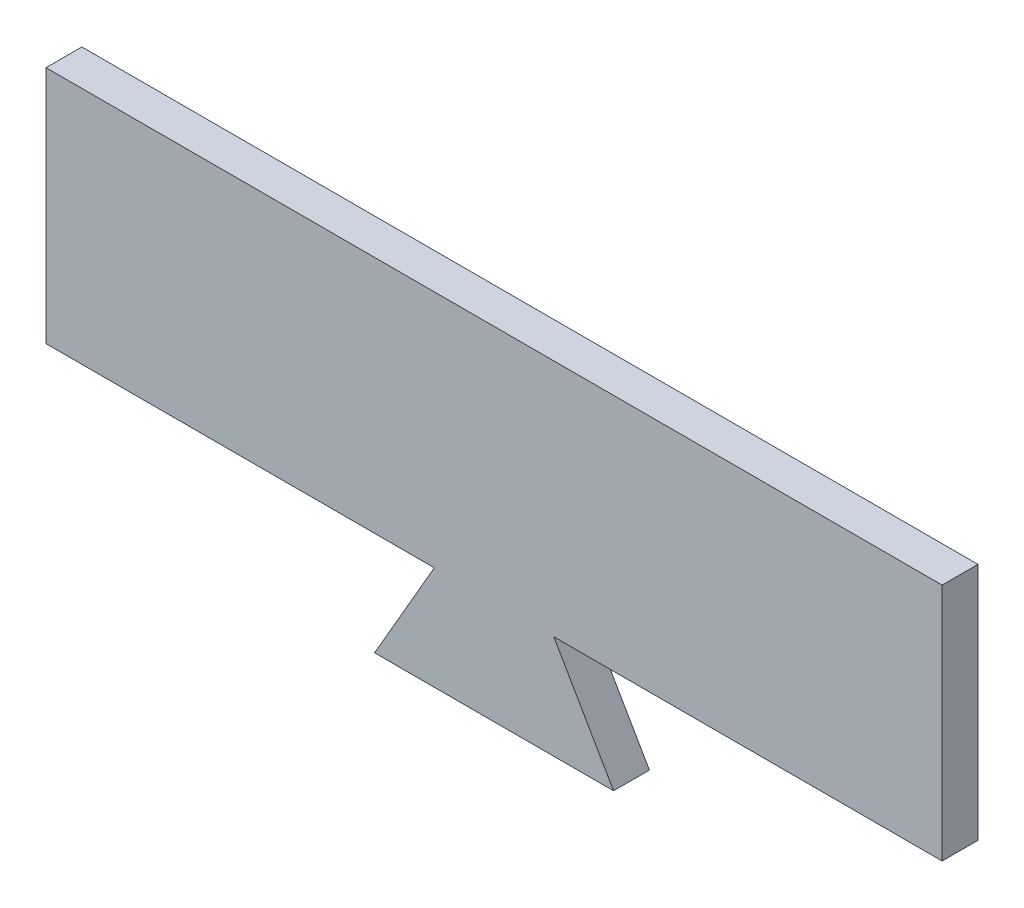
SolidWorks part; units mm, degrees
ref_plane "Plan de face" through (0, 0, 0) normal (0, 0, 1) x (1, 0, 0)
ref_plane "Plan de dessus" through (0, 0, 0) normal (0, 1, 0) x (1, 0, 0)
ref_plane "Plan de droite" through (0, 0, 0) normal (1, 0, 0) x (0, 0, -1)
sketch "Esquisse1" plane through (0, 0, 0) normal (0, 0, 1) x (1, 0, 0)
  line L0 (-80.0391, 74.2018) -> (69.9609, 74.2018)
  line L1 (69.9609, 74.2018) -> (69.9609, 34.2018)
  line L2 (69.9609, 34.2018) -> (4.9609, 34.2018)
  line L3 (4.9609, 34.2018) -> (14.9609, 16.8813)
  line L4 (14.9609, 16.8813) -> (-25.0391, 16.8813)
  line L5 (-25.0391, 16.8813) -> (-15.0391, 34.2018)
  line L6 (-15.0391, 34.2018) -> (-80.0391, 34.2018)
  line L7 (-80.0391, 34.2018) -> (-80.0391, 74.2018)
  dimension "D1" = 150
  dimension "D2" = 40
  dimension "D3" = 40
  dimension "D4" = 90
  dimension "D5" = 40
  dimension "D6" = 20
  dimension "D7" = 20
  dimension "D8" = 20
  dimension "D9" = 65
extrude "Boss.-Extru.1" add sketch "Esquisse1" along normal blind 6 contours L7 L0 L1 L2 L3 L4 L5 L6
